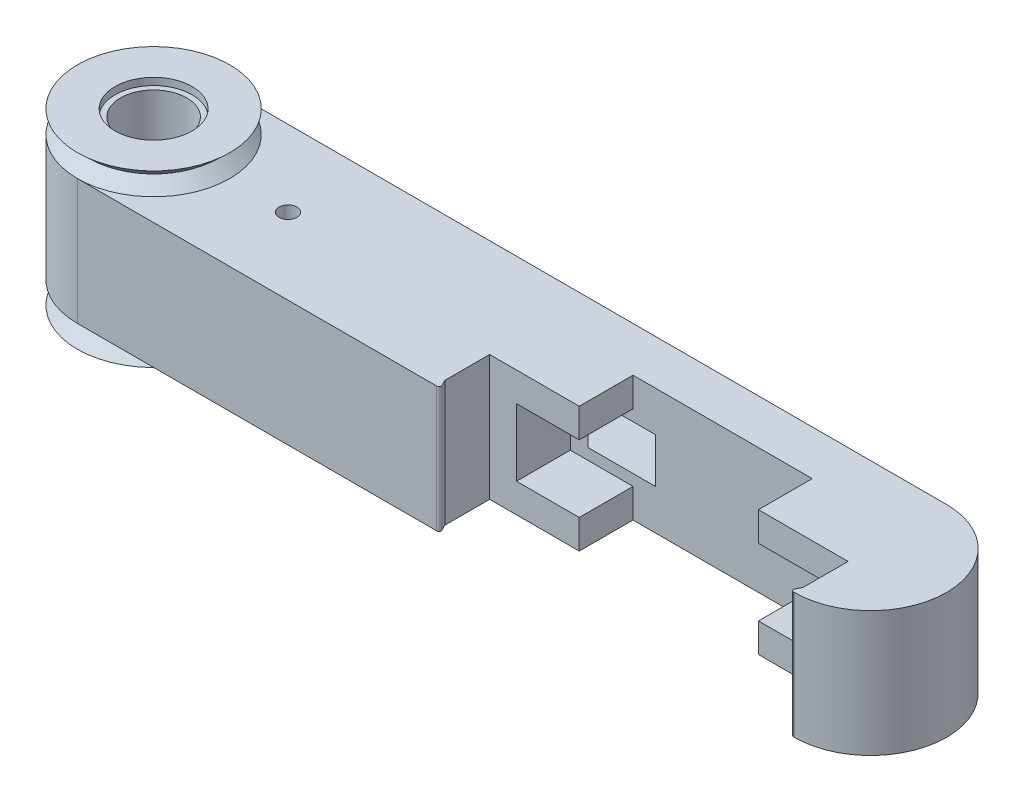
SolidWorks part; units mm, degrees
ref_plane "정면" through (0, 0, 0) normal (0, 0, 1) x (1, 0, 0)
ref_plane "윗면" through (0, 0, 0) normal (0, 1, 0) x (1, 0, 0)
ref_plane "우측면" through (0, 0, 0) normal (1, 0, 0) x (0, 0, -1)
sketch "스케치1" plane through (0, 0, 0) normal (0, 1, 0) x (1, 0, 0)
  line L0 (0, 0) -> (80, 0) construction
  line L1 (0, 8.5) -> (80, 8.5)
  line L2 (0, -8.5) -> (80, -8.5)
  arc A0 (0, 8.5) -> (0, -8.5) centre (0, 0) ccw
  arc A1 (80, -8.5) -> (80, 8.5) centre (80, 0) ccw
  point P3 (40, 0)
  dimension "D1" = 17
  dimension "D2" = 80
extrude "보스-돌출1" add sketch "스케치1" along normal blind 14
sketch "스케치2" plane through (0, 0, 0) normal (1, 0, 0) x (0, 0, -1)
  line L0 (0, 14) -> (0, 0) construction
  line L1 (8.5, 14) -> (-8.5, 14) construction
  line L2 (0, 14) -> (0, 16.5)
  line L3 (0, 55) -> (0, -55) construction
  line L4 (0, 16.5) -> (8.5, 16.5)
  line L5 (8.5, 16.5) -> (7.15, 15.25)
  line L6 (7.15, 15.25) -> (8.5, 14)
  line L7 (8.5, 14) -> (0, 14)
  line L8 (8.5, 14) -> (8.5, 0) construction
  line L9 (0, 0) -> (0, -2.5)
  line L10 (0, -2.5) -> (8.5, -2.5)
  line L11 (8.5, -2.5) -> (7.15, -1.25)
  line L12 (7.15, -1.25) -> (8.5, 0)
  line L13 (55, 0) -> (-55, 0) construction
  line L14 (8.5, 0) -> (0, 0)
  point P18 (0, 15.25)
  point P21 (0, -1.25)
  dimension "D1" = 2.5
  dimension "D2" = 7.15
  dimension "D3" = 2.5
  dimension "D4" = 7.15
revolve "회전1" add sketch "스케치2" angle 360 about L0
sketch "스케치3" plane through (0, 16.5, 0) normal (0, 1, 0) x (1, 0, 0)
  circle A0 centre (0, 0) radius 3.7
  dimension "D1" = 7.4
extrude "컷-돌출1" cut sketch "스케치3" against normal up to surface (19 mm away) up to face at (0, -2.5, 8.5)
sketch "스케치5" plane through (0, 16.5, 0) normal (0, 1, 0) x (1, 0, 0)
  circle A0 centre (0, 0) radius 4.3
  dimension "D1" = 8.6
sketch "스케치6" plane through (0, -2.5, 0) normal (0, -1, 0) x (1, 0, 0)
  circle A0 centre (0, 0) radius 4.3
  dimension "D1" = 8.6
extrude "컷-돌출2" cut sketch "스케치5" against normal blind 0.8
extrude "컷-돌출3" cut sketch "스케치6" against normal blind 0.8
sketch "스케치8" plane through (0, 0, 8.5) normal (0, 0, 1) x (1, 0, 0)
  line L0 (0, 0) -> (80, 0) construction
  line L1 (80, 14) -> (40, 14)
  line L2 (80, 14) -> (80, 0)
  line L3 (80, 0) -> (40, 0)
  line L4 (40, 14) -> (40, 0)
  dimension "D1" = 40
extrude "컷-돌출4" cut sketch "스케치8" against normal blind 12
sketch "스케치9" plane through (0, 0, -3.5) normal (0, 0, 1) x (1, 0, 0)
  line L1 (45, 9.5) -> (47.5, 9.5)
  line L2 (45, 9.5) -> (45, 4.5)
  line L3 (45, 4.5) -> (47.5, 4.5)
  line L4 (47.5, 9.5) -> (47.5, 4.5)
  line L5 (40, 14) -> (40, 0) construction
  line L6 (40, 14) -> (40, 0) construction
  point P8 (40, 7)
  point P9 (47.5, 7)
  dimension "D1" = 2.5
  dimension "D2" = 5
  dimension "D3" = 5
extrude "컷-돌출5" cut sketch "스케치9" against normal up to surface (5 mm away) up to face at (40, 7, -8.5)
sketch "스케치11" plane through (0, 4.5, 0) normal (0, 1, 0) x (1, 0, 0)
  line L0 (47.5, 3.5) -> (52.5, 3.5)
  line L1 (52.5, 3.5) -> (47.5, 8.5)
  line L2 (47.5, 8.5) -> (40, 8.5)
  line L3 (40, 8.5) -> (45, 3.5)
  line L4 (45, 3.5) -> (47.5, 3.5)
  dimension "D1" = 7.5
extrude "컷-돌출6" cut sketch "스케치11" along normal up to surface (5 mm away) up to face at (46.25, 9.5, -6)
sketch "스케치12" plane through (0, 0, -3.5) normal (0, 0, 1) x (1, 0, 0)
  line L0 (80, 14) -> (70, 14)
  line L1 (80, 14) -> (40, 14) construction
  line L2 (70, 14) -> (70, 10.75)
  line L3 (70, 10.75) -> (77, 10.75)
  line L4 (77, 10.75) -> (77, 3.25)
  line L5 (77, 3.25) -> (70, 3.25)
  line L6 (70, 3.25) -> (70, 0)
  line L7 (9.35, 0) -> (-9.35, 0) construction
  line L8 (70, 0) -> (80, 0)
  line L9 (80, 14) -> (80, 0) construction
  line L10 (80, 0) -> (80, 14)
  line L11 (50, 14) -> (50, 10.75)
  line L13 (50, 10.75) -> (43, 10.75)
  line L14 (43, 10.75) -> (43, 3.25)
  line L15 (43, 3.25) -> (50, 3.25)
  line L17 (50, 3.25) -> (50, 0)
  line L18 (40, 0) -> (80, 0) construction
  line L19 (50, 0) -> (40, 0)
  line L20 (40, 0) -> (40, 14)
  line L21 (40, 14) -> (50, 14)
  dimension "D1" = 3.25
  dimension "D2" = 3.25
  dimension "D3" = 3
  dimension "D4" = 3
  dimension "D5" = 10
extrude "보스-돌출3" add sketch "스케치12" along normal blind 6
sketch "스케치13" plane through (0, 14, 0) normal (0, 1, 0) x (1, 0, 0)
  line L0 (40, -7) -> (41, -8.5)
  line L1 (40, -2.5) -> (40, -8.5) construction
  line L2 (41, -8.5) -> (40, -8.5)
  line L3 (40, -8.5) -> (40, -7)
  line L4 (80, -7) -> (79, -8.5)
  line L5 (80, -2.5) -> (80, -8.5) construction
  line L6 (79, -8.5) -> (80, -8.5)
  line L7 (80, -8.5) -> (80, -7)
  dimension "D1" = 1
  dimension "D2" = 1
  dimension "D3" = 1.5
  dimension "D4" = 1.5
extrude "보스-돌출4" [suppressed] add sketch "스케치13" against normal up to surface (14 mm away)
sketch "스케치14" plane through (0, 0, 0) normal (0, -1, 0) x (1, 0, 0)
  line L0 (40, 8.5) -> (40.5, 8.5)
  line L1 (40.5, 8.5) -> (40, 7.5)
  line L2 (40, 2.5) -> (40, 8.5) construction
  line L3 (40, 7.5) -> (40, 8.5)
  line L4 (80, 8.5) -> (79.5, 8.5)
  line L5 (80, 2.5) -> (80, 8.5) construction
  line L6 (79.5, 8.5) -> (80, 7.5)
  line L7 (80, 7.5) -> (80, 8.5)
  arc A0 (80, -8.5) -> (80, 8.5) centre (80, 0) ccw construction
  dimension "D1" = 0.5
  dimension "D2" = 1
extrude "보스-돌출5" add sketch "스케치14" against normal up to surface (14 mm away) up to face at (52.4545, 14, 1.0455)
fillet "필렛5" radius 0.25 2 edges at (79.5, 7, 8.5) (40.5, 7, 8.5)
sketch "스케치15" plane through (0, 14, 0) normal (0, 1, 0) x (1, 0, 0)
  line L0 (-10.45, 0) -> (10.45, 0) construction
  circle A0 centre (15, 0) radius 1
  dimension "D2" = 2
  dimension "D1" = 15
extrude "컷-돌출7" cut sketch "스케치15" against normal up to surface (14 mm away) up to face at (56.0625, 0, 3.2126)
